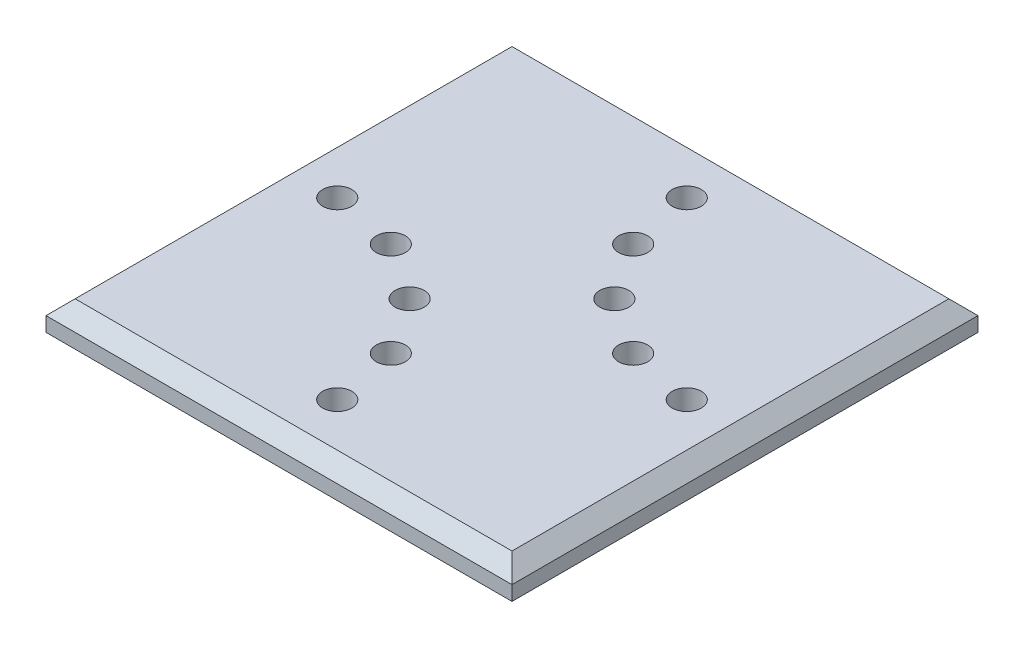
SolidWorks part; units mm, degrees
material "Al - 6061 Polished"
ref_plane "Front Plane" through (0, 0, 0) normal (0, 0, 1) x (1, 0, 0)
ref_plane "Top Plane" through (0, 0, 0) normal (0, 1, 0) x (1, 0, 0)
ref_plane "Right Plane" through (0, 0, 0) normal (1, 0, 0) x (0, 0, -1)
sketch "Sketch1" plane through (0, 0, 0) normal (0, 1, 0) x (1, 0, 0)
  line L2 (-50.8, -50.8) -> (50.8, -50.8)
  line L3 (-50.8, -50.8) -> (-50.8, 50.8)
  line L4 (-50.8, 50.8) -> (50.8, 50.8)
  line L5 (50.8, -50.8) -> (50.8, 50.8)
  line L6 (-50.8, -50.8) -> (50.8, 50.8) construction
  line L7 (-50.8, 50.8) -> (50.8, -50.8) construction
  point P2 (0, 0)
  dimension "D1" = 101.6
extrude "Boss-Extrude1" add sketch "Sketch1" along normal blind 9.525
sketch "Sketch2" plane through (0, 0, 0) normal (0, -1, 0) x (1, 0, 0)
  line L0 (47.498, 47.498) -> (-47.498, 47.498)
  line L1 (-47.498, 47.498) -> (-47.498, -47.498)
  line L2 (-47.498, -47.498) -> (47.498, -47.498)
  line L3 (47.498, -47.498) -> (47.498, 47.498)
  line L4 (50.8, -50.8) -> (50.8, 50.8)
  line L5 (50.8, 50.8) -> (-50.8, 50.8)
  line L6 (-50.8, 50.8) -> (-50.8, -50.8)
  line L7 (-50.8, -50.8) -> (50.8, -50.8)
  line L8 (50.8, -50.8) -> (50.8, 50.8)
  line L9 (50.8, 50.8) -> (-50.8, 50.8)
  line L10 (-50.8, 50.8) -> (-50.8, -50.8)
  line L11 (-50.8, -50.8) -> (50.8, -50.8)
  dimension "D1" = 0
  dimension "D2" = 3.302
extrude "Cut-Extrude1" cut sketch "Sketch2" against normal blind 3.175
chamfer "Chamfer1" distance 3.175 angle 45 4 edges at (0, 9.525, 50.8) (-50.8, 9.525, 0) (0, 9.525, -50.8) (50.8, 9.525, 0)
sketch "Sketch3" [suppressed] plane through (0, 9.525, 0) normal (0, 1, 0) x (1, 0, 0)
  line L0 (50.8, 50.8) -> (38.1, -38.1) construction
  line L1 (38.1, -38.1) -> (50.8, 50.8) construction
  line L2 (50.8, 50.8) -> (-38.1, 38.1) construction
  line L3 (38.1, 38.1) -> (38.1, -38.1) construction
  line L4 (38.1, 38.1) -> (38.1, -38.1) construction
  line L5 (38.1, -38.1) -> (114.3, -38.1) construction
  line L6 (38.1, -38.1) -> (38.1, 38.1) construction
  line L7 (38.1, -38.1) -> (21.1439, 36.1895) construction
  line L8 (-38.1, 38.1) -> (-38.1, -38.1) construction
  line L9 (-38.1, 38.1) -> (-21.1439, -36.1895) construction
  circle A0 centre (38.1, -38.1) radius 76.2 construction
  circle A3 centre (38.1, 38.1) radius 3.175 construction
  circle A4 centre (-38.1, 38.1) radius 76.2 construction
  circle A5 centre (21.1439, 36.1895) radius 3.175
  circle A6 centre (5.0381, 30.5538) radius 3.175
  circle A7 centre (-9.4099, 21.4756) radius 3.175
  circle A8 centre (-21.4756, 9.4099) radius 3.175
  circle A9 centre (-30.5538, -5.0381) radius 3.175
  circle A10 centre (-36.1895, -21.1439) radius 3.175
  circle A11 centre (-38.1, -38.1) radius 3.175
  circle A12 centre (-21.1439, -36.1895) radius 3.175
  circle A13 centre (-5.0381, -30.5538) radius 3.175
  circle A14 centre (9.4099, -21.4756) radius 3.175
  circle A15 centre (21.4756, -9.4099) radius 3.175
  circle A16 centre (30.5538, 5.0381) radius 3.175
  circle A17 centre (36.1895, 21.1439) radius 3.175
  circle A18 centre (38.1, 38.1) radius 3.175
  dimension "D5" = 152.4
  dimension "D6" = 6.35
  dimension "D1" = 88.9
  dimension "D2" = 12.7
  dimension "D3" = 88.9
  dimension "D4" = 12.7
  dimension "D7" = 90
  dimension "D9" = 12.857
  dimension "D11" = 12.857
  dimension "D8" = 8
  dimension "D10" = 8
extrude "Diana Hole Pattern" [suppressed] cut sketch "Sketch3" against normal through all
sketch "Sketch9" [suppressed] plane through (0, 0, 0) normal (0, 1, 0) x (1, 0, 0)
  circle A0 centre (0, 0) radius 3.175
  circle A11 centre (19.05, 0) radius 3.175
  circle A12 centre (0, -19.05) radius 3.175
  circle A13 centre (-19.05, 0) radius 3.175
  circle A14 centre (0, 19.05) radius 3.175
  circle A16 centre (38.1, 0) radius 3.175
  circle A17 centre (26.9408, -26.9408) radius 3.175
  circle A18 centre (0, -38.1) radius 3.175
  circle A19 centre (-26.9408, -26.9408) radius 3.175
  circle A20 centre (-38.1, 0) radius 3.175
  circle A21 centre (-26.9408, 26.9408) radius 3.175
  circle A22 centre (0, 38.1) radius 3.175
  circle A23 centre (26.9408, 26.9408) radius 3.175
  point P14 (0, 0)
  point P15 (0, 0)
  dimension "D1" = 6.35
  dimension "D3" = 4
  dimension "D2" = 19.05
  dimension "D4" = 38.1
  dimension "D5" = 8
sketch "Sketch10" [suppressed] plane through (0, 0, 0) normal (0, -1, 0) x (1, 0, 0)
extrude "Cut-Extrude3" [suppressed] cut sketch "Sketch9" along normal blind 55.118
sketch "Sketch11" plane through (0, 9.525, 0) normal (0, 1, 0) x (1, 0, 0)
  line L2 (50.8, 50.8) -> (50.8, -50.8) construction
  line L3 (-50.8, 50.8) -> (50.8, 50.8) construction
  line L4 (-38.1, -38.1) -> (0, 0) construction
  line L5 (-23.5198, -2.9002) -> (-38.1, -38.1) construction
  line L6 (-38.1, -38.1) -> (-2.9002, -23.5198) construction
  line L7 (-38.1, -38.1) -> (-38.1, 0) construction
  line L8 (-38.1, -38.1) -> (0, -38.1) construction
  line L9 (-47.625, 47.625) -> (47.625, -47.625) construction
  circle A1 centre (-38.1, -38.1) radius 3.175 construction
  circle A2 centre (-38.1, 0) radius 3.175
  circle A3 centre (0, -38.1) radius 3.175
  circle A4 centre (-11.1592, -11.1592) radius 3.175
  circle A5 centre (-38.1, -38.1) radius 38.1 construction
  circle A6 centre (-23.5198, -2.9002) radius 3.175
  circle A8 centre (-2.9002, -23.5198) radius 3.175
  circle A9 centre (38.1, 0) radius 3.175
  circle A10 centre (23.5198, 2.9002) radius 3.175
  circle A11 centre (11.1592, 11.1592) radius 3.175
  circle A12 centre (2.9002, 23.5198) radius 3.175
  circle A13 centre (0, 38.1) radius 3.175
  dimension "D1" = 88.9
  dimension "D2" = 6.35
  dimension "D6" = 38.1
  dimension "D7" = 45
  dimension "D3" = 88.9
  dimension "D4" = 38.1
  dimension "D5" = 38.1
  dimension "D8" = 22.5
extrude "Cut-Extrude4" cut sketch "Sketch11" against normal through all and the other way through all
